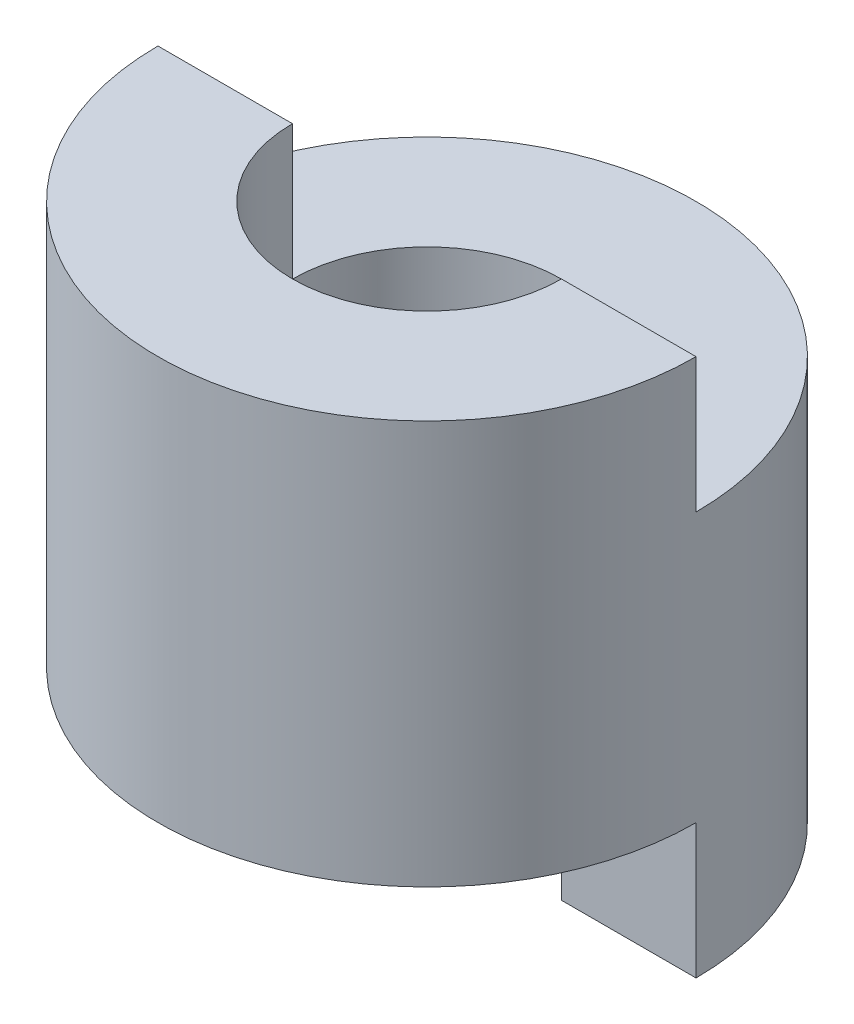
SolidWorks part; units mm, degrees
ref_plane "Front Plane" through (0, 0, 0) normal (0, 0, 1) x (1, 0, 0)
ref_plane "Top Plane" through (0, 0, 0) normal (0, 1, 0) x (1, 0, 0)
ref_plane "Right Plane" through (0, 0, 0) normal (1, 0, 0) x (0, 0, -1)
sketch "Sketch1" plane through (0, 0, 0) normal (0, 0, 1) x (1, 0, 0)
  line L1 (0, 0) -> (10, 0)
  line L2 (0, 0) -> (0, 20)
  line L3 (0, 20) -> (10, 20)
  line L4 (10, 0) -> (10, 20)
  dimension "D1" = 20
  dimension "D2" = 10
revolve "Revolve1" add sketch "Sketch1" angle 360 about L2
sketch "Sketch2" plane through (0, 20, 0) normal (0, 1, 0) x (1, 0, 0)
  circle A0 centre (0, 0) radius 5
  dimension "D1" = 10
extrude "Cut-Extrude1" cut sketch "Sketch2" against normal blind 20
sketch "Sketch3" plane through (0, 20, 0) normal (0, 1, 0) x (1, 0, 0)
  line L0 (-10, 0) -> (-5, 0)
  line L1 (5, 0) -> (10, 0)
  arc A0 (-10, 0) -> (10, 0) centre (0, 0) cw
  circle A1 centre (0, 0) radius 10 construction
  arc A2 (-5, 0) -> (5, 0) centre (0, 0) cw
  circle A3 centre (0, 0) radius 5 construction
  dimension "D3" = 5
  dimension "D4" = 10
  dimension "D1" = 5
  dimension "D2" = 5
extrude "Cut-Extrude2" cut sketch "Sketch3" against normal blind 5
sketch "Sketch4" plane through (0, 0, 0) normal (0, -1, 0) x (1, 0, 0)
  line L0 (-10, 0) -> (-5, 0)
  line L1 (5, 0) -> (10, 0)
  arc A0 (-10, 0) -> (10, 0) centre (0, 0) cw
  circle A1 centre (0, 0) radius 10 construction
  arc A2 (-5, 0) -> (5, 0) centre (0, 0) cw
  dimension "D1" = 5
  dimension "D2" = 10
extrude "Cut-Extrude3" cut sketch "Sketch4" against normal blind 5
